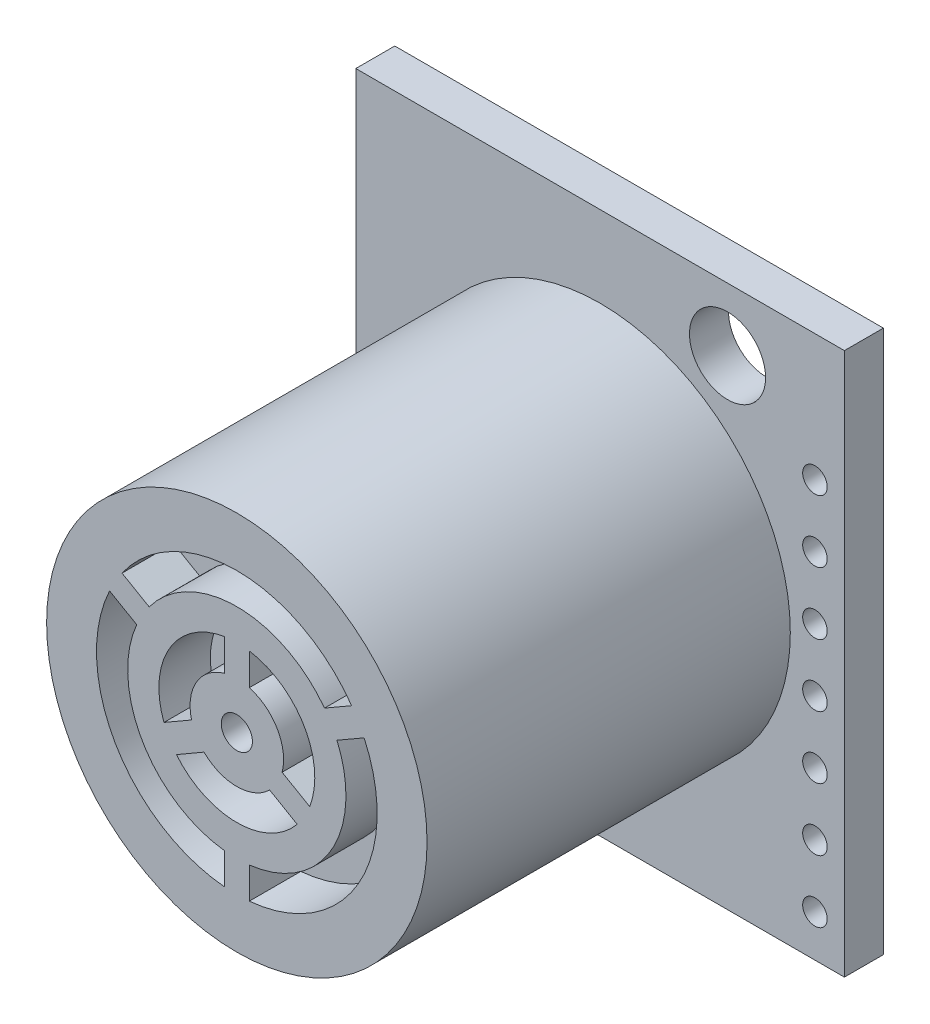
SolidWorks part; units mm, degrees
ref_plane "Front Plane" through (0, 0, 0) normal (0, 0, 1) x (1, 0, 0)
ref_plane "Top Plane" through (0, 0, 0) normal (0, 1, 0) x (1, 0, 0)
ref_plane "Right Plane" through (0, 0, 0) normal (1, 0, 0) x (0, 0, -1)
sketch "Sketch1" plane through (0, 0, 0) normal (0, 0, 1) x (1, 0, 0)
  line L1 (-9.95, -11.05) -> (9.95, -11.05)
  line L2 (-9.95, -11.05) -> (-9.95, 11.05)
  line L3 (-9.95, 11.05) -> (9.95, 11.05)
  line L4 (9.95, -11.05) -> (9.95, 11.05)
  line L5 (-9.95, -11.05) -> (9.95, 11.05) construction
  line L6 (-9.95, 11.05) -> (9.95, -11.05) construction
  point P0 (0, 0)
  dimension "D1" = 19.9
  dimension "D2" = 22.1
extrude "Extrude1" add sketch "Sketch1" along normal blind 1.5875
sketch "Sketch2" plane through (0, 0, 1.5875) normal (0, 0, 1) x (1, 0, 0)
  circle A0 centre (0, 0) radius 7.747
  dimension "D1" = 15.494
extrude "Extrude2" add sketch "Sketch2" along normal blind 14.7955 separate body
sketch "Sketch3" plane through (0, 0, 16.383) normal (0, 0, 1) x (1, 0, 0)
  line L0 (0, 1.905) -> (0, 7.747) construction
  line L1 (1.6498, -0.9525) -> (6.7091, -3.8735) construction
  line L2 (-1.6498, -0.9525) -> (-6.7091, -3.8735) construction
  line L3 (0.508, 1.836) -> (0.508, 3.1341)
  line L4 (-1.844, -0.4781) -> (-2.9682, -1.1271)
  line L5 (1.336, -1.3579) -> (2.4602, -2.007)
  line L6 (-0.508, 1.836) -> (-0.508, 3.1341)
  line L7 (-1.336, -1.3579) -> (-2.4602, -2.007)
  line L8 (1.844, -0.4781) -> (2.9682, -1.1271)
  line L9 (0, 0) -> (6.0492, 3.4925) construction
  line L10 (0.508, -4.4159) -> (0.508, -5.6924)
  line L11 (-0.508, -6.9665) -> (-0.508, -6.985)
  line L12 (0.508, -6.9665) -> (0.508, -6.985)
  line L13 (6.2872, 3.0433) -> (6.3032, 3.0526)
  line L14 (-0.508, -4.4159) -> (-0.508, -5.6924)
  line L15 (5.7792, 3.9232) -> (5.7952, 3.9324)
  line L16 (-6.2872, 3.0433) -> (-6.3032, 3.0526)
  line L19 (-4.0783, 1.768) -> (-5.1837, 2.4062)
  line L20 (-3.5703, 2.6479) -> (-4.6757, 3.2861)
  line L23 (3.5703, 2.6479) -> (4.6757, 3.2861)
  line L24 (4.0783, 1.768) -> (5.1837, 2.4062)
  line L27 (-5.7792, 3.9232) -> (-5.7952, 3.9324)
  circle A0 centre (0, 0) radius 0.635
  arc A1 (-0.508, 1.836) -> (-1.844, -0.4781) centre (0, 0) ccw
  arc A2 (-0.508, 3.1341) -> (-2.9682, -1.1271) centre (0, 0) ccw
  arc A3 (3.5703, 2.6479) -> (-3.5703, 2.6479) centre (0, 0) ccw
  arc A4 (0.508, -5.6924) -> (5.1837, 2.4062) centre (0, 0) ccw
  circle A5 centre (0, 0) radius 6.985
  circle A6 centre (0, 0) radius 7.747 construction
  circle A7 centre (0, 0) radius 1.905 construction
  arc A8 (-1.336, -1.3579) -> (1.336, -1.3579) centre (0, 0) ccw
  arc A9 (1.844, -0.4781) -> (0.508, 1.836) centre (0, 0) ccw
  circle A11 centre (0, 0) radius 3.175 construction
  arc A12 (-2.4602, -2.007) -> (2.4602, -2.007) centre (0, 0) ccw
  arc A13 (2.9682, -1.1271) -> (0.508, 3.1341) centre (0, 0) ccw
  circle A14 centre (0, 0) radius 4.445 construction
  arc A15 (-4.0783, 1.768) -> (-0.508, -4.4159) centre (0, 0) ccw
  arc A16 (0.508, -4.4159) -> (4.0783, 1.768) centre (0, 0) ccw
  circle A17 centre (0, 0) radius 5.715 construction
  arc A18 (4.6757, 3.2861) -> (-4.6757, 3.2861) centre (0, 0) ccw
  arc A19 (-5.1837, 2.4062) -> (-0.508, -5.6924) centre (0, 0) ccw
  dimension "D6" = 1.27
  dimension "D7" = 60
  dimension "D1" = 1.27
  dimension "D2" = 1.27
  dimension "D3" = 1.27
  dimension "D4" = 1.27
  dimension "D5" = 1.27
extrude "Extrude3" cut sketch "Sketch3" against normal blind 2.0955 contours L23 A18 L20 A3 | L19 A19 L14 A15 | L6 A2 L4 A1 | L7 A12 L5 A8 | A0 | L8 A13 L3 A9 | A16 L10 A4 L24
sketch "Sketch4" plane through (0, 0, 0) normal (0, 1, 0) x (1, 0, 0)
  line L0 (0, -16.383) -> (0, -397.383) construction
  line L1 (-7.747, -16.383) -> (7.747, -16.383) construction
  line L2 (0, -16.383) -> (276.8127, -397.383)
  line L3 (276.8127, -397.383) -> (0, -397.383)
  line L4 (0, -16.383) -> (0, -397.383)
  dimension "D1" = 36
  dimension "D2" = 381
revolve "Revolve1" [suppressed] add sketch "Sketch4" angle 360 about L0
sketch "Sketch5" plane through (0, 0, 1.5875) normal (0, 0, 1) x (1, 0, 0)
  line L0 (-9.95, 11.05) -> (-9.95, -11.05) construction
  line L1 (-9.95, -11.05) -> (9.95, -11.05) construction
  circle A0 centre (5.19, 8.49) radius 1.55
  circle A1 centre (-7.41, -8.51) radius 1.55
  dimension "D1" = 3.1
  dimension "D2" = 12.6
  dimension "D3" = 2.54
  dimension "D4" = 17
  dimension "D5" = 2.54
extrude "Cut-Extrude1" cut sketch "Sketch5" against normal through all
sketch "Sketch6" plane through (0, 0, 1.5875) normal (0, 0, 1) x (1, 0, 0)
  line L0 (-9.95, 11.05) -> (-9.95, -11.05) construction
  line L1 (-9.95, -11.05) -> (9.95, -11.05) construction
  circle A0 centre (8.75, 5.89) radius 0.5
  circle A1 centre (8.75, 3.35) radius 0.5
  circle A2 centre (8.75, 0.81) radius 0.5
  circle A3 centre (8.75, -1.73) radius 0.5
  circle A4 centre (8.75, -4.27) radius 0.5
  circle A5 centre (8.75, -6.81) radius 0.5
  circle A6 centre (8.75, -9.35) radius 0.5
  dimension "D2" = 1
  dimension "D5" = 2.54
  dimension "D1" = 18.7
  dimension "D4" = 1.7
  dimension "D3" = 7
extrude "Cut-Extrude2" cut sketch "Sketch6" against normal through all
